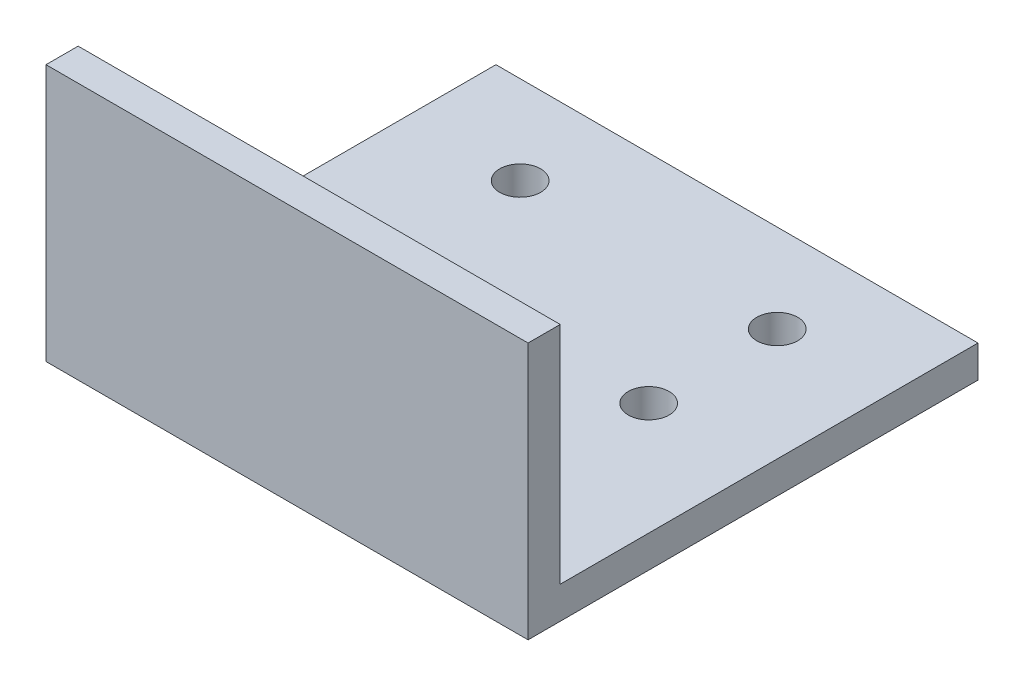
SolidWorks part; units mm, degrees
ref_plane "Front" through (0, 0, 0) normal (0, 0, 1) x (1, 0, 0)
ref_plane "Top" through (0, 0, 0) normal (0, 1, 0) x (1, 0, 0)
ref_plane "Right" through (0, 0, 0) normal (1, 0, 0) x (0, 0, -1)
sketch "Sketch1" plane through (0, 0, 0) normal (1, 0, 0) x (0, 0, -1)
  line L0 (3.175, 3.175) -> (3.175, 25.4)
  line L1 (0, 0) -> (44.45, 0)
  line L2 (0, 0) -> (0, 25.4)
  line L5 (3.175, 3.175) -> (44.45, 3.175)
  line L6 (0, 25.4) -> (3.175, 25.4)
  line L7 (44.45, 0) -> (44.45, 3.175)
  dimension "D1" = 25.4
  dimension "D2" = 44.45
  dimension "D3" = 3.175
extrude "Boss-Extrude1" add sketch "Sketch1" along normal blind 47.625
sketch "Sketch2" plane through (0, 3.175, 0) normal (0, 1, 0) x (1, 0, 0)
  circle A0 centre (11.1125, 23.029) radius 2.0193 construction
  circle A1 centre (11.1125, 23.029) radius 2.0193
  circle A2 centre (11.1125, 35.729) radius 2.0193 construction
  circle A3 centre (11.1125, 35.729) radius 2.0193
  circle A4 centre (36.5125, 23.029) radius 2.0193 construction
  circle A5 centre (36.5125, 23.029) radius 2.0193
  circle A6 centre (36.5125, 35.729) radius 2.0193 construction
  circle A7 centre (36.5125, 35.729) radius 2.0193
extrude "Cut-Extrude1" cut sketch "Sketch2" against normal up to next
